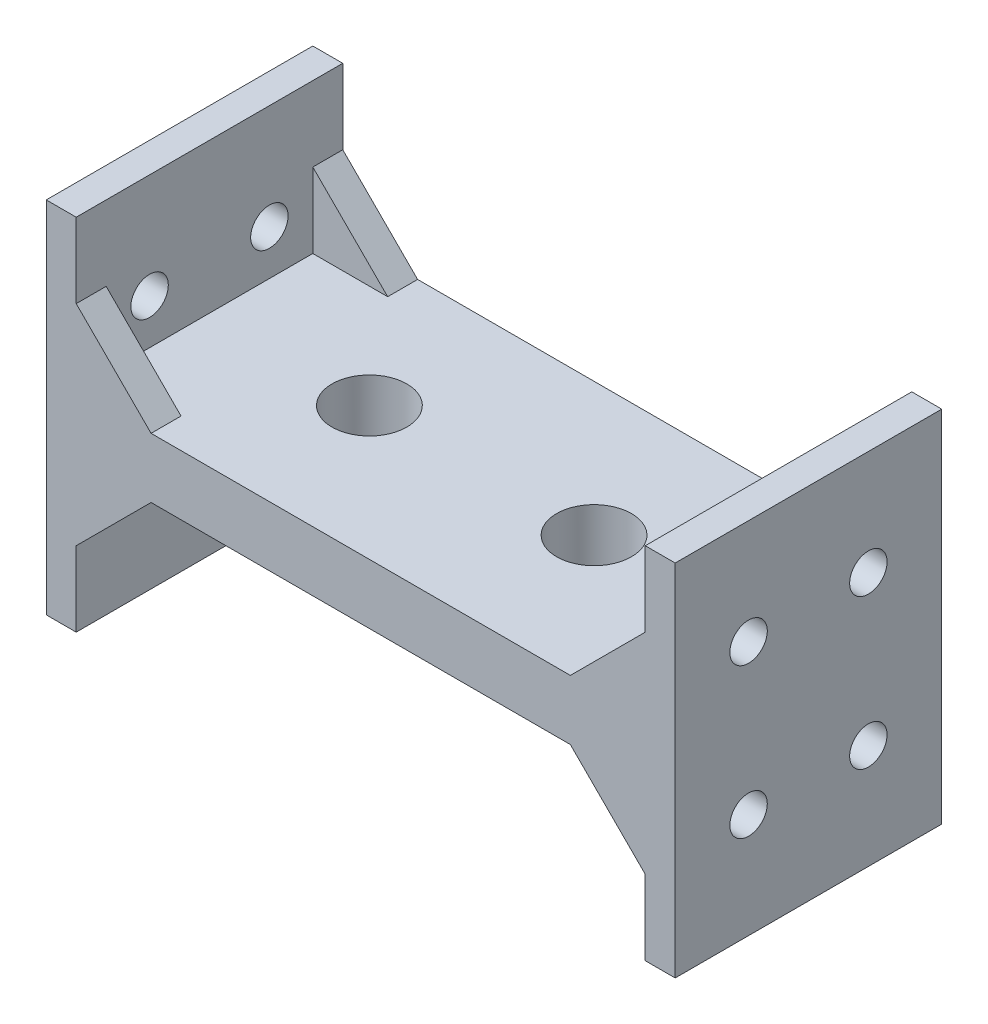
SolidWorks part; units mm, degrees
ref_plane "Front Plane" through (0, 0, 0) normal (0, 0, 1) x (1, 0, 0)
ref_plane "Top Plane" through (0, 0, 0) normal (0, 1, 0) x (1, 0, 0)
ref_plane "Right Plane" through (0, 0, 0) normal (1, 0, 0) x (0, 0, -1)
sketch "Sketch2" plane through (0, 0, 0) normal (0, 1, 0) x (1, 0, 0)
  line L1 (-21, 8.9) -> (21, 8.9)
  line L2 (-21, 8.9) -> (-21, -8.9)
  line L3 (-21, -8.9) -> (21, -8.9)
  line L4 (21, 8.9) -> (21, -8.9)
  line L5 (-21, 8.9) -> (21, -8.9) construction
  line L6 (-21, -8.9) -> (21, 8.9) construction
  point P0 (0, 0)
  dimension "D1" = 17.8
  dimension "D2" = 42
extrude "Boss-Extrude1" add sketch "Sketch2" along normal blind 4
sketch "Sketch3" plane through (0, 0, 0) normal (0, -1, 0) x (1, 0, 0)
  line L0 (21, -8.9) -> (-21, -8.9) construction
  line L1 (-21, 8.9) -> (-19, 8.9)
  line L2 (-21, 8.9) -> (-21, -8.9)
  line L3 (-21, -8.9) -> (-19, -8.9)
  line L4 (-19, 8.9) -> (-19, -8.9)
  line L5 (-21, 8.9) -> (21, 8.9) construction
  line L6 (21, 8.9) -> (19, 8.9)
  line L7 (21, 8.9) -> (21, -8.9)
  line L8 (21, -8.9) -> (19, -8.9)
  line L9 (19, 8.9) -> (19, -8.9)
  line L10 (21, 8.9) -> (21, -8.9) construction
  dimension "D1" = 2
  dimension "D2" = 2
extrude "Boss-Extrude2" add sketch "Sketch3" along normal blind 10
sketch "Sketch4" plane through (0, 0, 8.9) normal (0, 0, 1) x (1, 0, 0)
  line L0 (-19, 0) -> (19, 0) construction
  line L1 (-19, 0) -> (-14, 0)
  line L2 (-19, -10) -> (-19, 0) construction
  line L3 (-19, -5) -> (-19, 0)
  line L4 (-19, -5) -> (-14, 0)
  line L5 (0, 4) -> (0, 0) construction
  line L6 (-21, 4) -> (21, 4) construction
  line L7 (19, -5) -> (14, 0)
  line L8 (19, 0) -> (14, 0)
  line L9 (19, -5) -> (19, 0)
  dimension "D1" = 5
  dimension "D2" = 5
extrude "Boss-Extrude3" add sketch "Sketch4" against normal blind 2
mirror "Mirror1" about plane through (0, 0, 0) normal (0, 0, 1) of "Boss-Extrude3"
sketch "Sketch5" plane through (0, 0, 0) normal (0, -1, 0) x (1, 0, 0)
  line L0 (-19, 0) -> (19, 0) construction
  line L1 (-19, -8.9) -> (-19, 8.9) construction
  line L2 (19, 8.9) -> (19, -8.9) construction
  circle A0 centre (-8.3199, 0) radius 2.5
  circle A1 centre (6.6801, 0) radius 2.5
  dimension "D1" = 5
  dimension "D2" = 5
  dimension "D3" = 15
extrude "Cut-Extrude1" cut sketch "Sketch5" against normal through all both and the other way through all
sketch "Sketch6" plane through (-19, 0, 0) normal (1, 0, 0) x (0, 0, -1)
  line L0 (8.9, -10) -> (-8.9, -10) construction
  line L1 (0, 0) -> (0, -10) construction
  line L2 (6.9, 0) -> (-6.9, 0) construction
  circle A0 centre (-4, -3) radius 1.25
  circle A1 centre (4, -3) radius 1.25
  dimension "D1" = 2.5
  dimension "D2" = 2.5
  dimension "D3" = 8
  dimension "D4" = 3
  dimension "D5" = 3
  dimension "D6" = 4
extrude "Cut-Extrude2" cut sketch "Sketch6" against normal blind 2
mirror "Mirror2" about plane through (0, 0, 0) normal (1, 0, 0) of "Cut-Extrude2"
sketch "Sketch7" plane through (0, 4, 0) normal (0, 1, 0) x (1, 0, 0)
  line L0 (-21, -8.9) -> (21, -8.9) construction
  line L1 (-21, 8.9) -> (-19, 8.9)
  line L2 (-21, 8.9) -> (-21, -8.9)
  line L3 (-21, -8.9) -> (-19, -8.9)
  line L4 (-19, 8.9) -> (-19, -8.9)
  line L6 (21, 8.9) -> (19, 8.9)
  line L7 (21, 8.9) -> (21, -8.9)
  line L8 (21, -8.9) -> (19, -8.9)
  line L9 (19, 8.9) -> (19, -8.9)
  dimension "D1" = 2
  dimension "D2" = 2
extrude "Boss-Extrude4" add sketch "Sketch7" along normal blind 10
sketch "Sketch8" plane through (-19, 0, 0) normal (1, 0, 0) x (0, 0, -1)
  line L0 (0, 14) -> (0, 4) construction
  line L1 (-8.9, 14) -> (8.9, 14) construction
  line L2 (-8.9, 4) -> (8.9, 4) construction
  line L3 (-8.9, 9) -> (8.9, 9) construction
  line L4 (-8.9, 14) -> (-8.9, 4) construction
  line L5 (8.9, 14) -> (8.9, 4) construction
  circle A0 centre (-4, 7) radius 1.25
  circle A1 centre (4, 7) radius 1.25
  dimension "D3" = 2.5
  dimension "D4" = 2.5
  dimension "D1" = 8
  dimension "D2" = 4
  dimension "D5" = 3
  dimension "D6" = 3
extrude "Cut-Extrude3" cut sketch "Sketch8" against normal blind 10
mirror "Mirror3" about plane through (0, 0, 0) normal (1, 0, 0) of "Cut-Extrude3"
sketch "Sketch9" plane through (0, 0, -8.9) normal (0, 0, -1) x (-1, 0, 0)
  line L0 (-19, 14) -> (-19, 4) construction
  line L1 (-19, 9) -> (-19, 4)
  line L2 (-19, 4) -> (19, 4) construction
  line L3 (-19, 4) -> (-14, 4)
  line L4 (-19, 9) -> (-14, 4)
  line L5 (0, 4) -> (0, 0) construction
  line L6 (19, 9) -> (14, 4)
  line L7 (19, 4) -> (14, 4)
  line L8 (19, 9) -> (19, 4)
  dimension "D1" = 5
  dimension "D2" = 5
extrude "Boss-Extrude5" add sketch "Sketch9" against normal blind 2
mirror "Mirror4" about plane through (0, 0, 0) normal (0, 0, 1) of "Boss-Extrude5"
